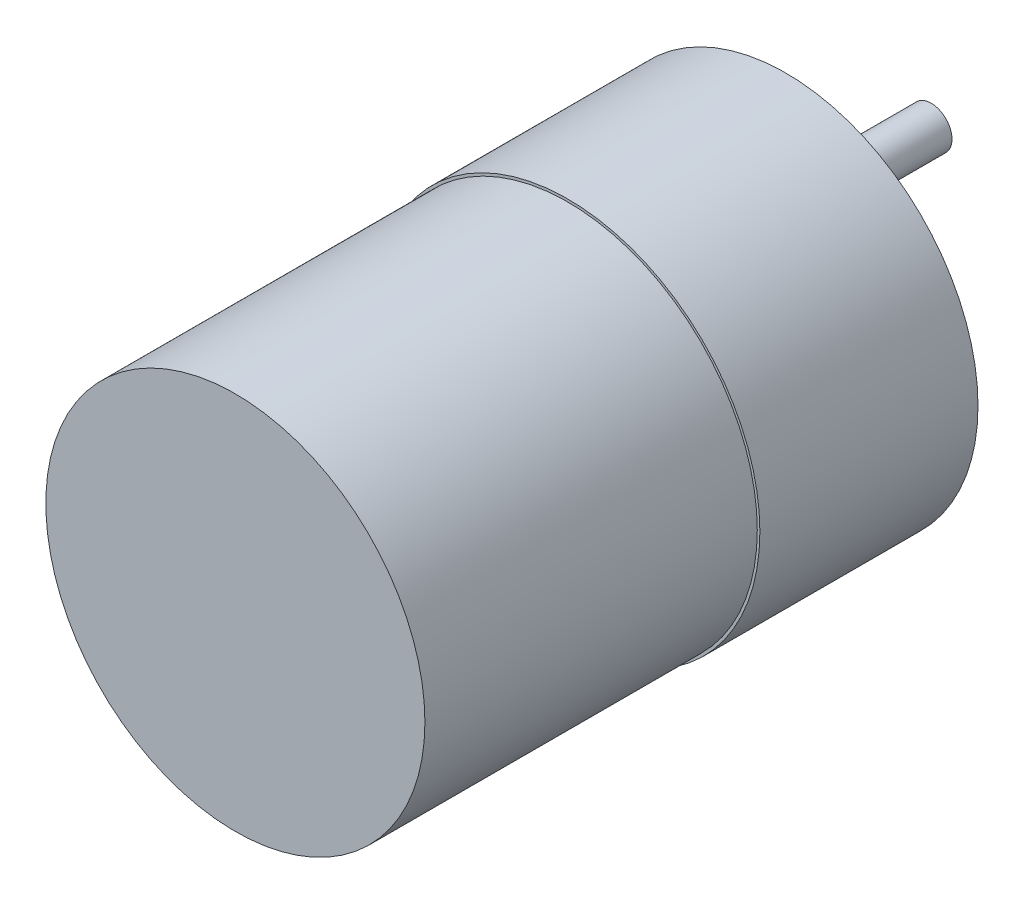
SolidWorks part; units mm, degrees
ref_plane "Plano frontal" through (0, 0, 0) normal (0, 0, 1) x (1, 0, 0)
ref_plane "Plano superior" through (0, 0, 0) normal (0, 1, 0) x (1, 0, 0)
ref_plane "Plano direito" through (0, 0, 0) normal (1, 0, 0) x (0, 0, -1)
sketch "Model" plane through (0, 0, 0) normal (0, 0, 1) x (1, 0, 0)
  circle A0 centre (20.777, -9.842) radius 1.25
  circle A1 centre (23.953, 0) radius 1.25
  circle A2 centre (20.777, 9.842) radius 1.25
  circle A3 centre (7.003, 16.95) radius 1.25
  circle A4 centre (-6.771, 9.842) radius 1.25
  circle A5 centre (-6.771, -9.842) radius 1.25
  circle A6 centre (7.003, -16.95) radius 1.25
  circle A7 centre (0, 0) radius 6
  circle A9 centre (7.003, 0.02) radius 18.5
  dimension "D2" = 2.5
  dimension "D3" = 12
  dimension "D4" = 6.771
  dimension "D16" = 2.5
  dimension "D17" = 2.5
  dimension "D18" = 2.5
  dimension "D19" = 2.5
  dimension "D20" = 2.5
  dimension "D21" = 2.5
  dimension "D23" = 37
  dimension "D1" = 9.842
  dimension "D5" = 9.842
  dimension "D6" = 6.771
  dimension "D7" = 16.95
  dimension "D8" = 16.95
  dimension "D9" = 20.777
  dimension "D10" = 9.842
  dimension "D11" = 7.003
  dimension "D12" = 7.003
  dimension "D13" = 20.777
  dimension "D14" = 9.842
  dimension "D15" = 23.953
  dimension "D24" = 7.003
extrude "Ressalto-extrusão1" add sketch "Model" along normal blind 21
sketch "Esboço2" plane through (0, 0, 21) normal (0, 0, 1) x (1, 0, 0)
  circle A0 centre (7.003, 0.02) radius 18.25
  dimension "D1" = 36.5
extrude "Ressalto-extrusão5" add sketch "Esboço2" along normal blind 32 contours A0
sketch "Esboço3" plane through (0, 0, 21) normal (0, 0, -1) x (-1, 0, 0)
  circle A0 centre (0, 0) radius 6
extrude "Ressalto-extrusão6" add sketch "Esboço3" along normal blind 27
sketch "Esboço4" plane through (0, 0, -6) normal (0, 0, -1) x (-1, 0, 0)
  circle A0 centre (0, 0) radius 2
  dimension "D1" = 4
extrude "Ressalto-extrusão7" add sketch "Esboço4" along normal blind 15
